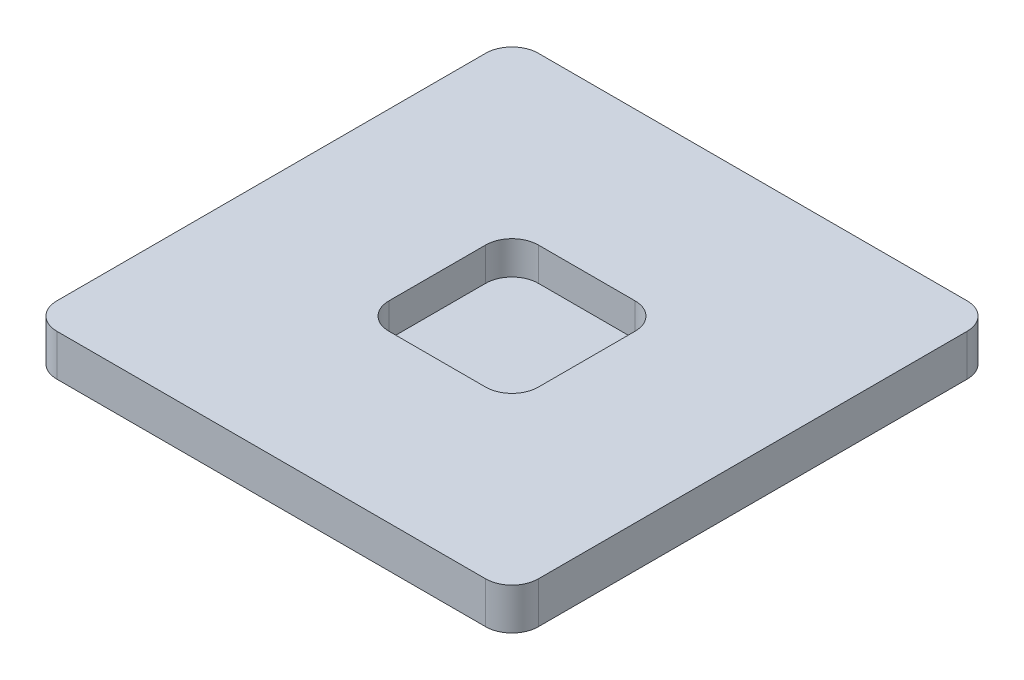
SolidWorks part; units mm, degrees
ref_plane "Front Plane" through (0, 0, 0) normal (0, 0, 1) x (1, 0, 0)
ref_plane "Top Plane" through (0, 0, 0) normal (0, 1, 0) x (1, 0, 0)
ref_plane "Right Plane" through (0, 0, 0) normal (1, 0, 0) x (0, 0, -1)
sketch "Sketch1" plane through (0, 0, 0) normal (0, 1, 0) x (1, 0, 0)
  line L1 (0, 0) -> (29, 0)
  line L2 (0, 0) -> (0, 29)
  line L3 (0, 29) -> (29, 29)
  line L4 (29, 0) -> (29, 29)
  dimension "D1" = 29
extrude "Boss-Extrude1" add sketch "Sketch1" along normal blind 7.5
sketch "Sketch8" plane through (0, 7.5, 0) normal (0, 1, 0) x (1, 0, 0)
  line L0 (14.5, 19) -> (14.5, 29) construction
  line L1 (10, 19) -> (19, 19)
  line L2 (10, 19) -> (10, 10)
  line L3 (10, 10) -> (19, 10)
  line L4 (19, 19) -> (19, 10)
  line L5 (29, 29) -> (0, 29) construction
  line L6 (19, 14.5) -> (29, 14.5) construction
  line L7 (29, 0) -> (29, 29) construction
  dimension "D1" = 9
extrude "Cut-Extrude3" cut sketch "Sketch8" against normal blind 2
sketch "Sketch9" plane through (0, 0, 0) normal (0, -1, 0) x (1, 0, 0)
  line L0 (14.5, -7) -> (14.5, 0) construction
  line L1 (7, -7) -> (22, -7)
  line L2 (7, -7) -> (7, -22)
  line L3 (7, -22) -> (22, -22)
  line L4 (0, 0) -> (0, -29)
  line L5 (0, -29) -> (29, -29)
  line L6 (29, -29) -> (29, 0)
  line L7 (29, 0) -> (0, 0)
  line L8 (0, 0) -> (0, -29)
  line L9 (0, -29) -> (29, -29)
  line L10 (29, -29) -> (29, 0)
  line L11 (29, 0) -> (0, 0)
  line L12 (22, -7) -> (22, -22)
  line L13 (22, -14.5) -> (29, -14.5) construction
  dimension "D2" = 15
  dimension "D1" = 0
extrude "Cut-Extrude4" cut sketch "Sketch9" against normal blind 5
sketch "Sketch10" plane through (0, 0, 0) normal (0, -1, 0) x (1, 0, 0)
  line L4 (22, -7) -> (7, -7) construction
  line L5 (12.75, -7) -> (16.25, -7)
  line L6 (12.75, -7) -> (12.75, -8.8254)
  line L7 (12.75, -22) -> (16.25, -22)
  line L8 (16.25, -7) -> (16.25, -8.8254)
  line L9 (7, -22) -> (22, -22) construction
  line L10 (7, -7) -> (7, -22) construction
  line L11 (7, -12.75) -> (8.8254, -12.75)
  line L12 (7, -12.75) -> (7, -16.25)
  line L13 (7, -16.25) -> (8.8254, -16.25)
  line L14 (22, -12.75) -> (22, -16.25)
  line L15 (22, -22) -> (22, -7) construction
  line L16 (20.1746, -12.75) -> (22, -12.75)
  line L17 (20.1746, -16.25) -> (22, -16.25)
  line L18 (16.25, -20.1746) -> (16.25, -22)
  line L19 (12.75, -20.1746) -> (12.75, -22)
  line L20 (7, -7) -> (7, -22) construction
  line L21 (12.75, -8.8254) -> (8.8254, -12.75)
  line L22 (8.8254, -16.25) -> (12.75, -20.1746)
  line L23 (16.25, -20.1746) -> (20.1746, -16.25)
  line L24 (20.1746, -12.75) -> (16.25, -8.8254)
  line L25 (14.5, -7.2522) -> (14.5, -7) construction
  line L26 (21.7478, -14.5) -> (22, -14.5) construction
  line L27 (14.5, -21.7478) -> (14.5, -22) construction
  line L28 (22, -22) -> (22, -7) construction
  point P27 (7, -14.5)
  point P28 (7, -14.5)
  dimension "D1" = 3.5
  dimension "D2" = 10.5
  dimension "D3" = 45
  dimension "D4" = 45
extrude "Cut-Extrude5" cut sketch "Sketch10" against normal blind 2
fillet "Fillet1" radius 1.5875 16 edges at (16.25, 1, -8.8254) (20.1746, 1, -12.75) (20.1746, 1, -16.25) (16.25, 1, -20.1746) (12.75, 1, -20.1746) (8.8254, 1, -16.25) (8.8254, 1, -12.75) (12.75, 1, -8.8254) (0, 6.25, 0) (29, 6.25, 0) (29, 6.25, -29) (0, 6.25, -29) (10, 6.5, -10) (19, 6.5, -10) (19, 6.5, -19) (10, 6.5, -19)
